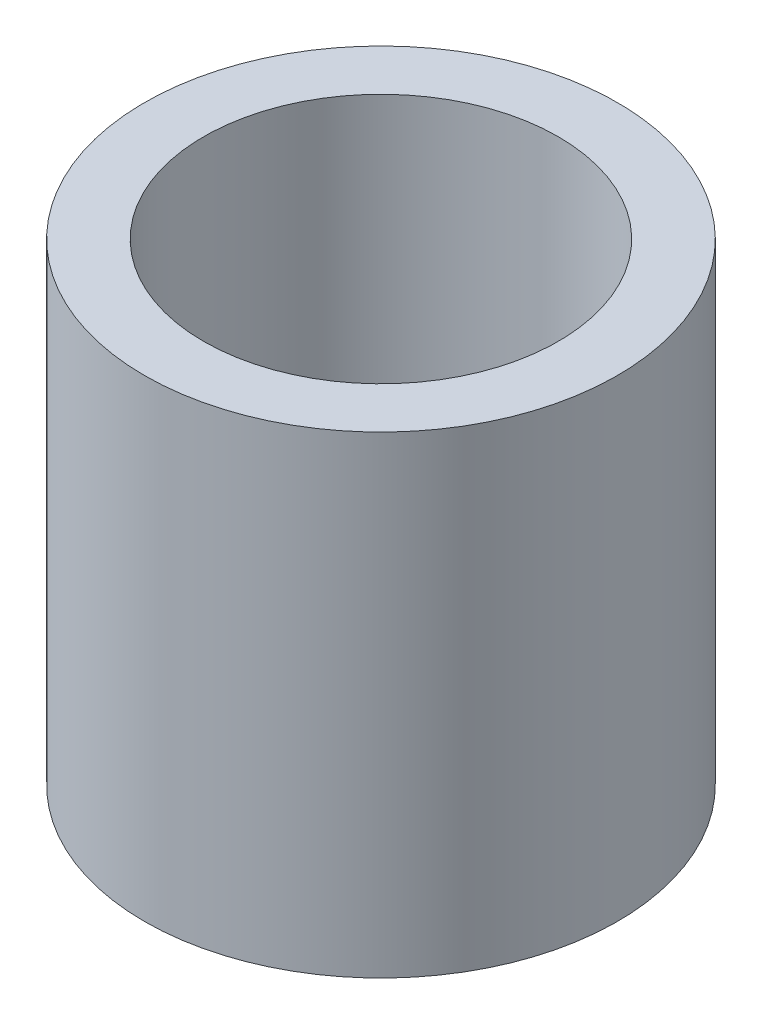
SolidWorks part; units mm, degrees
material "Brass"
ref_plane "Front Plane" through (0, 0, 0) normal (0, 0, 1) x (1, 0, 0)
ref_plane "Top Plane" through (0, 0, 0) normal (0, 1, 0) x (1, 0, 0)
ref_plane "Right Plane" through (0, 0, 0) normal (1, 0, 0) x (0, 0, -1)
sketch "Sketch1" plane through (0, 0, 0) normal (0, 1, 0) x (1, 0, 0)
  circle A0 centre (0, 0) radius 1.5
  circle A1 centre (0, 0) radius 2
  dimension "D1" = 3
  dimension "D2" = 4
extrude "Boss-Extrude1" add sketch "Sketch1" along normal blind 4
